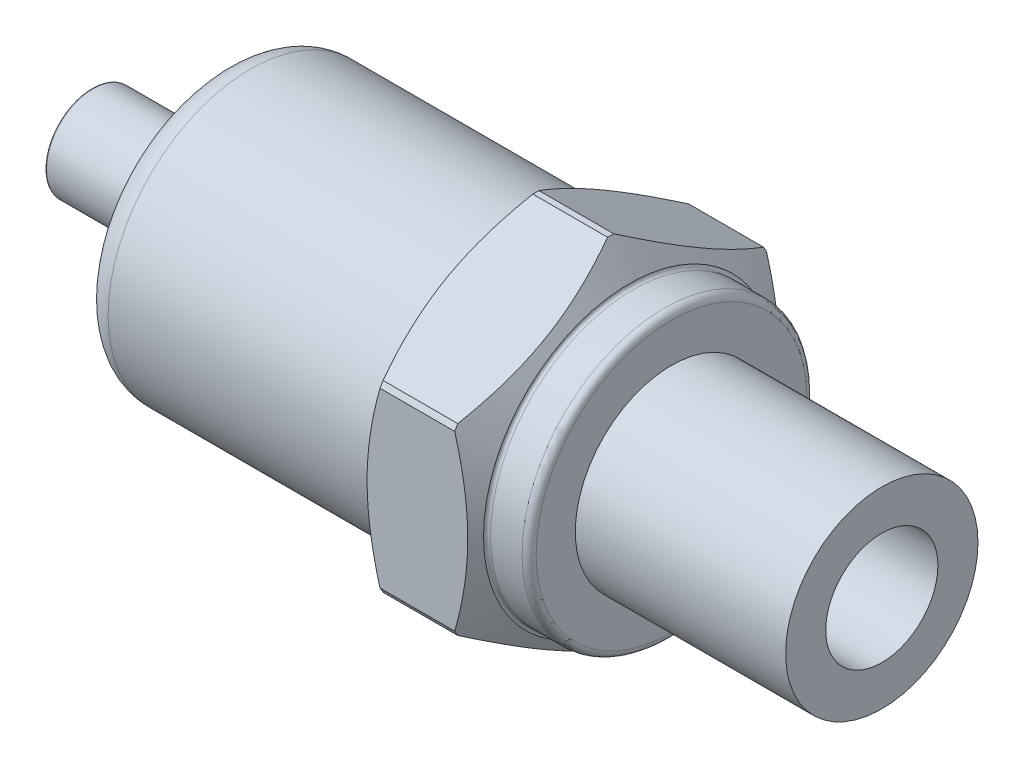
SolidWorks part; units mm, degrees
material "AISI 316 Stainless Steel Sheet (SS)"
ref_plane "Front Plane" through (0, 0, 0) normal (0, 0, 1) x (1, 0, 0)
ref_plane "Top Plane" through (0, 0, 0) normal (0, 1, 0) x (1, 0, 0)
ref_plane "Right Plane" through (0, 0, 0) normal (1, 0, 0) x (0, 0, -1)
sketch "Sketch1" plane through (0, 0, 0) normal (1, 0, 0) x (0, 0, -1)
  line L1 (11.115, -6.4172) -> (11.115, 6.4172)
  line L2 (11.115, 6.4172) -> (0, 12.8345)
  line L3 (0, 12.8345) -> (-11.115, 6.4172)
  line L4 (-11.115, 6.4172) -> (-11.115, -6.4172)
  line L5 (-11.115, -6.4172) -> (0, -12.8345)
  line L6 (0, -12.8345) -> (11.115, -6.4172)
  circle A0 centre (0, 0) radius 11.115 construction
  dimension "D1" = 22.23
extrude "Boss-Extrude1" add sketch "Sketch1" along normal blind 8
sketch "Sketch2" plane through (8, 0, 0) normal (1, 0, 0) x (0, 0, -1)
  circle A0 centre (0, 0) radius 10.15
  dimension "D1" = 20.3
extrude "Boss-Extrude2" add sketch "Sketch2" along normal blind 3
sketch "Sketch3" plane through (0, 0, 0) normal (-1, 0, 0) x (0, 0, 1)
  circle A0 centre (0, 0) radius 10.15
  dimension "D1" = 20.3
extrude "Boss-Extrude3" add sketch "Sketch3" along normal blind 20.32
sketch "Sketch4" plane through (-20.32, 0, 0) normal (-1, 0, 0) x (0, 0, 1)
  circle A1 centre (0, 0) radius 3.335
  dimension "D1" = 6.67
extrude "Boss-Extrude4" add sketch "Sketch4" along normal blind 3
loft "Loft1" add section edge at (-20.32, 0, 10.15) section edge at (-23.32, 0, 3.335)
sketch "Sketch6" plane through (-23.32, 0, 0) normal (-1, 0, 0) x (0, 0, 1)
  circle A0 centre (0, 0) radius 3.335
extrude "Boss-Extrude5" add sketch "Sketch6" along normal blind 7 contours A0
fillet "Fillet1" radius 0.1 1 edges at (-30.32, 0, 3.335)
fillet "Fillet2" radius 0.5 1 edges at (-23.32, 0, 3.335)
fillet "Fillet3" radius 2 1 edges at (-20.32, 0, 10.15)
fillet "Fillet4" radius 0.25 2 edges at (0, 0, 10.15) (8, 0, -10.15)
chamfer "Chamfer1" distance 0.25 angle 30 6 edges at (4, 6.4172, 11.115) (4, -6.4172, 11.115) (4, -12.8345, 0) (4, -6.4172, -11.115) (4, 6.4172, -11.115) (4, 12.8345, 0)
sketch "Sketch7" plane through (11, 0, 0) normal (1, 0, 0) x (0, 0, -1)
  circle A0 centre (0, 0) radius 6.858
  dimension "D1" = 13.716
extrude "Boss-Extrude6" add sketch "Sketch7" along normal blind 15
thread "Thread1" pitch 1.4111 start angle 0, offset 0, length 15, pitch 1.4111, diameter 13.716
ref_plane "Plane1" through (11, 0, -6.858) normal (0, -1, 0) x (0, 0, -1)
sketch "Thread Profile1" plane through (11, 0, -6.858) normal (0, -1, 0) x (0, 0, -1)
  line L0 (0, 0) -> (0, 1.4111) construction
  line L11 (0, 0) -> (0, 1.2347)
  line L12 (0, 1.2347) -> (-0.7638, 0.7937)
  line L13 (-0.7638, 0.7937) -> (-0.7638, 0.441)
  line L15 (-0.7638, 0.441) -> (0, 0)
  line L17 (-0.7638, 0.6174) -> (0, 0.6174) construction
  point P2 (0, 0)
  dimension "Pitch" = 1.4111
  dimension "Profile_Angle" = 60
  dimension "Profile_Land" = 0.3528
  dimension "Profile_Height" = 0.7638
sketch "Sketch12" plane through (26, 0, 0) normal (1, 0, 0) x (0, 0, -1)
  circle A0 centre (0, 0) radius 4
  dimension "D1" = 8
extrude "Cut-Extrude1" cut sketch "Sketch12" against normal blind 15
fillet "Fillet5" radius 0.5 1 edges at (11, 0, -10.15)
sketch "Sketch13" plane through (-30.32, 0, 0) normal (-1, 0, 0) x (0, 0, 1)
  circle A0 centre (0, 0) radius 2.2453
extrude "Cut-Extrude2" cut sketch "Sketch13" against normal blind 7
sketch "Sketch14" plane through (8, 0, 0) normal (1, 0, 0) x (0, 0, -1)
  circle A0 centre (0, 0) radius 10.4
extrude "Cut-Extrude5" cut sketch "Sketch14" against normal blind 10 draft 60 flip side to cut
sketch "Sketch15" plane through (0, 0, 0) normal (-1, 0, 0) x (0, 0, 1)
  circle A0 centre (0, 0) radius 10.4
extrude "Cut-Extrude6" cut sketch "Sketch15" against normal blind 10 draft 60 flip side to cut
